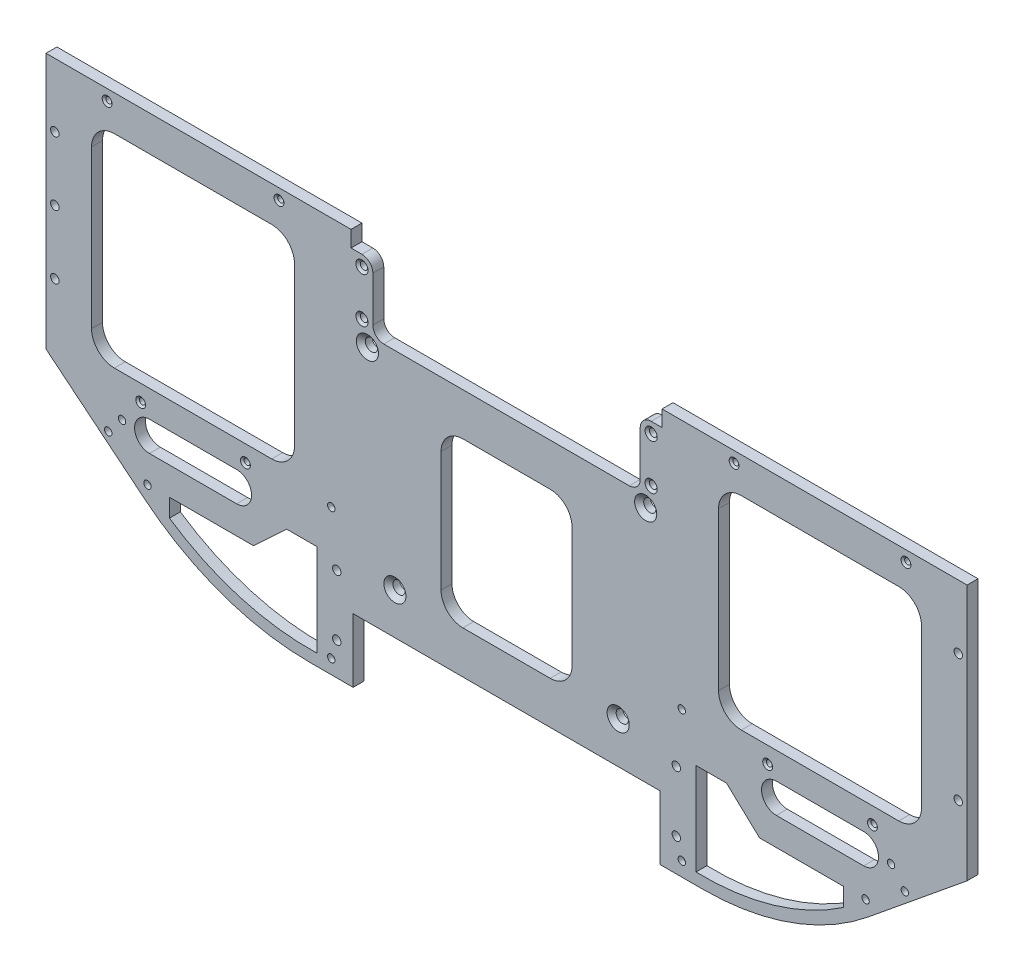
SolidWorks part; units mm, degrees
material "Acrylic (Medium-high impact)"
ref_plane "Front Plane" through (0, 0, 0) normal (0, 0, 1) x (1, 0, 0)
ref_plane "Top Plane" through (0, 0, 0) normal (0, 1, 0) x (1, 0, 0)
ref_plane "Right Plane" through (0, 0, 0) normal (1, 0, 0) x (0, 0, -1)
sketch "Sketch1" plane through (0, 0, 0) normal (0, 0, 1) x (1, 0, 0)
  line L0 (-85.5662, -233.3625) -> (-68.1037, -233.3625) construction
  line L1 (131.2863, 23.8125) -> (131.2863, -87.3125) construction
  line L2 (85.5663, 23.8125) -> (131.2863, 23.8125) construction
  line L3 (85.5663, -144.4625) -> (85.5663, 23.8125) construction
  line L6 (-79.2163, -3.175) -> (79.2162, -3.175) construction
  line L7 (-296.7037, -233.3625) -> (-68.1037, -233.3625)
  line L8 (131.2863, 23.8125) -> (131.2863, -87.3125)
  line L9 (85.5663, 23.8125) -> (131.2863, 23.8125)
  line L10 (85.5663, -3.175) -> (85.5663, 23.8125)
  line L11 (-131.6037, 20.5105) -> (-233.2037, 20.5105)
  line L12 (-131.6037, -3.175) -> (-131.6037, 20.5105)
  line L13 (-131.6037, -3.175) -> (85.5663, -3.175)
  line L14 (95.0913, -144.4625) -> (28.2786, -199.0142)
  line L15 (-182.4037, -196.215) -> (-182.4037, -51.435) construction
  line L16 (-93.5037, -196.215) -> (-271.3037, -196.215) construction
  line L17 (-268.1287, -51.435) -> (-96.6787, -51.435) construction
  line L18 (-459.8987, -144.4625) -> (-393.0861, -199.0142)
  line L19 (-233.2037, -3.175) -> (-450.3737, -3.175)
  line L20 (-233.2037, -3.175) -> (-233.2037, 20.5105)
  line L21 (-450.3737, -3.175) -> (-450.3737, -20.955)
  line L22 (-450.3737, -20.955) -> (-496.0937, -20.955)
  line L23 (-496.0937, -20.955) -> (-496.0937, -87.3125)
  line L24 (-496.0937, -20.955) -> (-450.3737, -20.955) construction
  line L25 (-450.3737, -20.955) -> (-450.3737, -144.4625) construction
  line L26 (-496.0937, -87.3125) -> (-496.0937, -20.955) construction
  arc A0 (-68.1037, -233.3625) -> (28.2786, -199.0142) centre (-68.1037, -80.9625) ccw construction
  arc A1 (95.0913, -144.4625) -> (131.2863, -87.3125) centre (-12.3507, -36.3792) ccw construction
  arc A2 (-68.1037, -233.3625) -> (28.2786, -199.0142) centre (-68.1037, -80.9625) ccw
  arc A3 (95.0913, -144.4625) -> (131.2863, -87.3125) centre (-12.3507, -36.3792) ccw
  arc A4 (-459.8987, -144.4625) -> (-496.0937, -87.3125) centre (-352.4568, -36.3792) cw
  arc A5 (-296.7037, -233.3625) -> (-393.0861, -199.0142) centre (-296.7037, -80.9625) cw
  point P39 (-182.4037, 20.5105)
  point P41 (-182.4037, -233.3625)
extrude "Boss-Extrude1" add sketch "Sketch1" along normal blind 6.35
sketch "Sketch2" plane through (0, 0, 6.35) normal (0, 0, 1) x (1, 0, 0)
  line L0 (-339.4075, -166.116) -> (-390.2075, -166.116) construction
  line L4 (-423.8625, -37.0786) -> (-423.8625, -128.6564)
  line L5 (-319.0186, -23.8125) -> (-410.5964, -23.8125)
  line L6 (-305.7525, -128.6564) -> (-305.7525, -37.0786)
  line L7 (-410.5964, -141.9225) -> (-319.0186, -141.9225)
  line L8 (-423.8625, -37.0786) -> (-423.8625, -128.6564)
  line L9 (-319.0186, -23.8125) -> (-410.5964, -23.8125)
  line L10 (-305.7525, -128.6564) -> (-305.7525, -37.0786)
  line L11 (-410.5964, -141.9225) -> (-319.0186, -141.9225)
  line L13 (-292.6397, -180.7374) -> (-292.6397, -217.9755) construction
  line L14 (-292.6397, -172.9769) -> (-292.6397, -226.6383)
  line L15 (-325.6433, -187.2504) -> (-310.3471, -172.9769) construction
  line L16 (-370.6622, -190.9763) -> (-337.9694, -190.9763) construction
  line L17 (-329.6361, -190.9763) -> (-310.3471, -172.9769)
  line L18 (-378.5543, -190.9763) -> (-329.6361, -190.9763)
  line L19 (-310.3471, -172.9769) -> (-292.6397, -172.9769)
  line L20 (-378.5543, -201.538) -> (-378.5543, -190.9763)
  line L21 (-339.4075, -174.752) -> (-390.2075, -174.752)
  line L24 (-339.4075, -157.48) -> (-390.2075, -157.48)
  line L25 (-182.4037, 20.5105) -> (-182.4037, -233.3625) construction
  line L26 (-131.6037, 20.5105) -> (-233.2037, 20.5105) construction
  line L29 (-296.7037, -233.3625) -> (-68.1037, -233.3625) construction
  line L30 (-25.4, -166.116) -> (25.4, -166.116) construction
  line L31 (-25.4, -174.752) -> (25.4, -174.752)
  line L32 (-25.4, -157.48) -> (25.4, -157.48)
  line L33 (13.7468, -201.538) -> (13.7468, -190.9763)
  line L34 (-54.4604, -172.9769) -> (-72.1678, -172.9769)
  line L35 (13.7468, -190.9763) -> (-35.1714, -190.9763)
  line L36 (-35.1714, -190.9763) -> (-54.4604, -172.9769)
  line L37 (-72.1678, -172.9769) -> (-72.1678, -226.6383)
  line L38 (45.7889, -141.9225) -> (-45.7889, -141.9225)
  line L39 (-59.055, -128.6564) -> (-59.055, -37.0786)
  line L40 (-45.7889, -23.8125) -> (45.7889, -23.8125)
  line L41 (59.055, -37.0786) -> (59.055, -128.6564)
  arc A4 (-423.8625, -128.6564) -> (-410.5964, -141.9225) centre (-410.5964, -128.6564) ccw
  arc A5 (-410.5964, -23.8125) -> (-423.8625, -37.0786) centre (-410.5964, -37.0786) ccw
  arc A6 (-305.7525, -37.0786) -> (-319.0186, -23.8125) centre (-319.0186, -37.0786) ccw
  arc A7 (-319.0186, -141.9225) -> (-305.7525, -128.6564) centre (-319.0186, -128.6564) ccw
  arc A8 (-423.8625, -128.6564) -> (-410.5964, -141.9225) centre (-410.5964, -128.6564) ccw
  arc A9 (-410.5964, -23.8125) -> (-423.8625, -37.0786) centre (-410.5964, -37.0786) ccw
  arc A10 (-305.7525, -37.0786) -> (-319.0186, -23.8125) centre (-319.0186, -37.0786) ccw
  arc A11 (-319.0186, -141.9225) -> (-305.7525, -128.6564) centre (-319.0186, -128.6564) ccw
  arc A13 (-339.4075, -174.752) -> (-339.4075, -157.48) centre (-339.4075, -166.116) ccw
  arc A15 (-373.3334, -204.9216) -> (-339.4598, -220.2819) centre (-296.7037, -80.9625) ccw construction
  arc A17 (-378.5543, -201.538) -> (-292.6397, -226.6383) centre (-296.7037, -80.9625) ccw
  arc A19 (-390.2075, -157.48) -> (-390.2075, -174.752) centre (-390.2075, -166.116) ccw
  arc A20 (-25.4, -174.752) -> (-25.4, -157.48) centre (-25.4, -166.116) cw
  arc A21 (25.4, -157.48) -> (25.4, -174.752) centre (25.4, -166.116) cw
  arc A22 (13.7468, -201.538) -> (-72.1678, -226.6383) centre (-68.1038, -80.9625) cw
  arc A23 (-45.7889, -141.9225) -> (-59.055, -128.6564) centre (-45.7889, -128.6564) cw
  arc A24 (-59.055, -37.0786) -> (-45.7889, -23.8125) centre (-45.7889, -37.0786) cw
  arc A25 (45.7889, -23.8125) -> (59.055, -37.0786) centre (45.7889, -37.0786) cw
  arc A26 (59.055, -128.6564) -> (45.7889, -141.9225) centre (45.7889, -128.6564) cw
  point P10 (-364.8075, -166.116)
  point P27 (0, -166.116)
  dimension "D2" = 8.636
  dimension "D3" = 50.8
  dimension "D1" = 0
extrude "Cut-Extrude1" cut sketch "Sketch2" against normal through all
hole_wizard "CSK for 1/4 Flat Head Machine Screw (100)1" positions "Sketch3" profile "Sketch4" countersink size "1/4" standard "ANSI Inch" end condition up to next
sketch "Sketch3" plane through (0, 0, 6.35) normal (0, 0, 1) x (1, 0, 0)
  point P0 (-247.3642, -172.085)
  point P3 (-263.3662, -57.785)
  point P6 (-117.4432, -172.085)
  point P9 (-101.4412, -57.785)
sketch "Sketch4" plane through (-247.3642, -172.085, 6.35) normal (1, 0, 0) x (0, -1, 0)
  line L0 (0, 0) -> (0, 6.35)
  line L1 (0, 6.35) -> (3.5712, 6.35)
  line L2 (3.5712, 6.35) -> (3.5712, 2.4063)
  line L3 (3.5712, 2.4063) -> (6.4389, 0)
  line L5 (6.4389, 0) -> (0, 0)
  line L6 (-3.5712, 2.4063) -> (-6.4389, 0) construction
  line L11 (0, -6.35) -> (0, 107.95) construction
  dimension "Thru Hole Dia." = 7.1425
  dimension "Thru Hole Depth" = 6.35
  dimension "Near C'Sink Dia." = 12.8778
  dimension "Near C'Sink Angle" = 100
hole_wizard "CSK for #4 Flat Head Machine Screw (100)1" positions "Sketch5" profile "Sketch6" countersink size "#4" standard "ANSI Inch" end condition through all
sketch "Sketch5" plane through (0, 0, 6.35) normal (0, 0, 1) x (1, 0, 0)
  point P0 (-334.3275, -151.5305)
  point P3 (-395.2875, -151.5305)
  point P6 (-314.8013, -9.525)
  point P9 (-414.8137, -9.525)
  point P12 (30.48, -151.5305)
  point P15 (-30.48, -151.5305)
  point P18 (50.0062, -9.525)
  point P21 (-50.0062, -9.525)
sketch "Sketch6" plane through (-334.3275, -151.5305, 6.35) normal (1, 0, 0) x (0, -1, 0)
  line L0 (0, 0) -> (0, 6.35)
  line L1 (0, 6.35) -> (1.7272, 6.35)
  line L2 (1.7272, 6.35) -> (1.7272, 0.9484)
  line L3 (1.7272, 0.9484) -> (2.8575, 0)
  line L5 (2.8575, 0) -> (0, 0)
  line L6 (-1.7272, 0.9484) -> (-2.8575, 0) construction
  line L11 (0, -6.35) -> (0, 107.95) construction
  dimension "Thru Hole Dia." = 3.4544
  dimension "Thru Hole Depth" = 6.35
  dimension "Near C'Sink Dia." = 5.715
  dimension "Near C'Sink Angle" = 100
sketch "Sketch7" plane through (0, 0, 6.35) normal (0, 0, 1) x (1, 0, 0)
  line L0 (-271.672, -233.3625) -> (-271.672, -196.215)
  line L1 (-271.672, -196.215) -> (-93.1354, -196.215)
  line L2 (-182.4037, -196.215) -> (-182.4037, -233.3625) construction
  line L3 (-296.7037, -233.3625) -> (-68.1037, -233.3625) construction
  line L4 (-93.5037, -196.215) -> (-271.3037, -196.215) construction
  line L5 (-93.1354, -233.3625) -> (-271.672, -233.3625)
  line L6 (-93.1354, -233.3625) -> (-93.1354, -196.215)
extrude "Cut-Extrude2" cut sketch "Sketch7" against normal up to next
hole_wizard "#6 Clearance Hole1" positions "Sketch21" profile "Sketch31" hole size "#6" standard "ANSI Inch" end condition up to next
sketch "Sketch21" plane through (-452.3171, -175.5643, 0) normal (0, 0, -1) x (-1, 0, 0)
  point P0 (-60.9984, -15.4755)
  point P3 (-167.9324, -49.5432)
  point P6 (-167.9324, 26.727)
  point P9 (-371.8944, 26.727)
  point P12 (-371.8944, -49.5432)
  point P15 (-478.8284, -15.4755)
sketch "Sketch31" plane through (-391.3187, -191.0398, 0) normal (1, 0, 0) x (0, 1, 0)
  line L0 (0, 0) -> (0, 6.35)
  line L1 (0, 6.35) -> (2.1526, 6.35)
  line L2 (2.1526, 6.35) -> (2.1526, 0)
  line L5 (2.1526, 0) -> (0, 0)
  line L11 (0, -6.35) -> (0, 107.95) construction
  dimension "Thru Hole Dia." = 4.3053
  dimension "Thru Hole Depth" = 6.35
hole_wizard "#6 Plastic Insert" positions "Sketch41" profile "Sketch51" legacy
sketch "Sketch41" plane through (-452.3171, -175.5643, 0) normal (0, 0, -1) x (-1, 0, 0)
  point P0 (-60.9984, -15.4755)
  point P3 (-167.9324, -49.5432)
  point P6 (-167.9324, 26.727)
  point P9 (-371.8944, 26.727)
  point P12 (-371.8944, -49.5432)
  point P15 (-478.8284, -15.4755)
sketch "Sketch51" plane through (-391.3187, -191.0398, 0) normal (1, 0, 0) x (0, 1, 0)
  line L0 (0, 0) -> (0, 3.81)
  line L1 (0, 3.81) -> (2.5273, 3.81)
  line L2 (2.5273, 3.81) -> (2.6543, 0)
  line L3 (2.6543, 0) -> (0, 0)
  line L4 (0, 110) -> (0, -10) construction
  dimension "Minor Diameter" = 5.0546
  dimension "Depth" = 3.81
  dimension "Major Diameter" = 5.3086
other "#6 Plastic Insert Hole<1>"
hole_wizard "#6 Clearance Hole2" positions "Sketch52" profile "Sketch53" hole size "#6" standard "ANSI Inch" end condition through all
sketch "Sketch52" plane through (0, 0, 0) normal (0, 0, -1) x (-1, 0, 0)
  point P0 (459.5177, -126.1745)
  point P3 (479.9012, -91.8845)
  point P6 (486.5052, -36.449)
  point P9 (-94.7103, -126.1745)
  point P12 (-121.9518, -83.6295)
  point P15 (-98.2663, 15.875)
sketch "Sketch53" plane through (-459.5177, -126.1745, 0) normal (1, 0, 0) x (0, 1, 0)
  line L0 (0, 0) -> (0, 6.35)
  line L1 (0, 6.35) -> (2.1526, 6.35)
  line L2 (2.1526, 6.35) -> (2.1526, 0)
  line L5 (2.1526, 0) -> (0, 0)
  line L11 (0, -6.35) -> (0, 107.95) construction
  dimension "Thru Hole Dia." = 4.3053
  dimension "Thru Hole Depth" = 6.35
sketch "Sketch54" plane through (0, 0, 6.35) normal (0, 0, 1) x (1, 0, 0)
  line L0 (-91.9162, -51.435) -> (-272.8912, -51.435) construction
  line L1 (-93.5037, -49.8475) -> (-271.3037, -49.8475) construction
  line L2 (-93.5037, -49.8475) -> (-93.5037, 20.5105) construction
  line L3 (-93.5037, 20.5105) -> (-271.3037, 20.5105) construction
  line L4 (-271.3037, -49.8475) -> (-271.3037, 20.5105) construction
  line L7 (-131.6037, 20.5105) -> (-233.2037, 20.5105) construction
  line L8 (-272.8912, -38.735) -> (-260.1912, -38.735)
  line L9 (-260.1912, -51.435) -> (-260.1912, -38.735)
  line L10 (-104.6162, -51.435) -> (-260.1912, -51.435)
  line L11 (-272.8912, -38.735) -> (-272.8912, 22.098)
  line L12 (-91.9162, 22.098) -> (-272.8912, 22.098)
  line L13 (-91.9162, -38.735) -> (-91.9162, 22.098)
  line L14 (-272.8912, -51.435) -> (-272.8912, 22.098) construction
  line L17 (-91.9162, -38.735) -> (-104.6162, -38.735)
  line L18 (-104.6162, -51.435) -> (-104.6162, -38.735)
  line L19 (-91.9162, -51.435) -> (-91.9162, 22.098) construction
  dimension "D1" = 1.5875
  dimension "D2" = 12.7
  dimension "D3" = 12.7
  dimension "D4" = 12.7
  dimension "D5" = 12.7
extrude "Cut-Extrude3" cut sketch "Sketch54" against normal up to next
sketch "Sketch55" plane through (0, 0, 6.35) normal (0, 0, 1) x (1, 0, 0)
  line L0 (-91.9162, -38.735) -> (-91.9162, -3.175) construction
  line L1 (-91.9162, -12.572) -> (-104.6162, -12.572)
  line L2 (-91.9162, -12.572) -> (-91.9162, -38.735)
  line L3 (-91.9162, -38.735) -> (-104.6162, -38.735)
  line L4 (-104.6162, -12.572) -> (-104.6162, -38.735)
  line L6 (-182.4037, -51.435) -> (-182.4037, -196.215) construction
  line L7 (-260.1912, -51.435) -> (-104.6162, -51.435) construction
  line L8 (-93.1354, -196.215) -> (-271.672, -196.215) construction
  line L9 (-260.1912, -12.572) -> (-260.1912, -38.735)
  line L10 (-272.8912, -38.735) -> (-260.1912, -38.735)
  line L11 (-272.8912, -12.572) -> (-272.8912, -38.735)
  line L12 (-272.8912, -12.572) -> (-260.1912, -12.572)
  line L13 (-93.5037, -9.397) -> (-134.7787, -9.397) construction
  dimension "D1" = 12.7
  dimension "D2" = 3.175
extrude "Boss-Extrude2" add sketch "Sketch55" against normal through all
fillet "Fillet3" radius 6.35 4 edges at (-104.6162, -12.572, 3.175) (-104.6162, -51.435, 3.175) (-260.1912, -51.435, 3.175) (-260.1912, -12.572, 3.175)
hole_wizard "CSK for #6 Flat Head Machine Screw (100)1" positions "Sketch56" profile "Sketch57" countersink size "#6" standard "ANSI Inch" end condition through all
sketch "Sketch56" plane through (0, 0, 6.35) normal (0, 0, 1) x (1, 0, 0)
  line L0 (-110.5963, -40.514) -> (-110.5963, -49.8475) construction
  line L2 (-95.0912, -49.8475) -> (-161.4487, -49.8475) construction
  line L3 (-103.0287, -40.514) -> (-110.5963, -40.514) construction
  line L4 (-110.5963, -45.1807) -> (-98.2662, -45.1807) construction
  point P0 (-266.5412, -18.922)
  point P8 (-98.2662, -18.922)
  point P31 (-98.2662, -45.1807)
  point P32 (-266.5412, -45.1807)
sketch "Sketch57" plane through (-266.5412, -18.922, 6.35) normal (1, 0, 0) x (0, -1, 0)
  line L0 (0, 0) -> (0, 6.35)
  line L1 (0, 6.35) -> (2.1526, 6.35)
  line L2 (2.1526, 6.35) -> (2.1526, 1.1669)
  line L3 (2.1526, 1.1669) -> (3.5433, 0)
  line L5 (3.5433, 0) -> (0, 0)
  line L6 (-2.1526, 1.1669) -> (-3.5433, 0) construction
  line L11 (0, -6.35) -> (0, 107.95) construction
  dimension "Thru Hole Dia." = 4.3053
  dimension "Thru Hole Depth" = 6.35
  dimension "Near C'Sink Dia." = 7.0866
  dimension "Near C'Sink Angle" = 100
sketch "Sketch58" plane through (0, 0, 6.35) normal (0, 0, 1) x (1, 0, 0)
  line L1 (-201.4537, -123.825) -> (-163.3537, -123.825) construction
  line L2 (-144.3037, -171.45) -> (-220.5037, -171.45)
  line L3 (-144.3037, -171.45) -> (-144.3037, -76.2)
  line L4 (-144.3037, -76.2) -> (-220.5037, -76.2)
  line L5 (-182.4037, -95.25) -> (-182.4037, -152.4) construction
  line L6 (-163.3537, -95.25) -> (-163.3537, -152.4) construction
  line L7 (-201.4537, -95.25) -> (-201.4537, -152.4) construction
  line L8 (-220.5037, -171.45) -> (-220.5037, -76.2)
  line L9 (-144.3037, -171.45) -> (-220.5037, -76.2) construction
  line L10 (-144.3037, -76.2) -> (-220.5037, -171.45) construction
  arc A0 (-163.3537, -95.25) -> (-201.4537, -95.25) centre (-182.4037, -95.25) ccw construction
  arc A1 (-201.4537, -152.4) -> (-163.3537, -152.4) centre (-182.4037, -152.4) ccw construction
  point P0 (-182.4037, -123.825)
  point P9 (-182.4037, -123.825)
  dimension "D1" = 57.15
  dimension "D2" = 38.1
  dimension "D3" = 76.2
extrude "Cut-Extrude4" cut sketch "Sketch58" against normal through all
sketch "Sketch60" plane through (0, 0, 6.35) normal (0, 0, 1) x (1, 0, 0)
  line L0 (85.5663, 23.8125) -> (85.5663, -152.2395)
  line L1 (28.2786, -199.0142) -> (95.0913, -144.4625) construction
  line L2 (131.2863, 23.8125) -> (85.5663, 23.8125) construction
  line L3 (131.2863, -87.3125) -> (131.2863, 23.8125) construction
  line L4 (131.2863, 23.8125) -> (85.5663, 23.8125)
  line L5 (131.2863, -87.3125) -> (131.2863, 23.8125)
  line L6 (85.5663, -152.2395) -> (95.0913, -144.4625)
  line L7 (-450.3737, -20.955) -> (-496.0937, -20.955) construction
  line L8 (-496.0937, -20.955) -> (-496.0937, -87.3125) construction
  line L9 (-459.8987, -144.4625) -> (-393.0861, -199.0142) construction
  line L10 (-450.3737, -20.955) -> (-496.0937, -20.955)
  line L11 (-496.0937, -20.955) -> (-496.0937, -87.3125)
  line L12 (-459.8987, -144.4625) -> (-450.3737, -152.2395)
  line L13 (-450.3737, -20.955) -> (-450.3737, -152.2395)
  arc A0 (95.0913, -144.4625) -> (131.2863, -87.3125) centre (-12.3507, -36.3792) ccw construction
  arc A1 (95.0913, -144.4625) -> (131.2863, -87.3125) centre (-12.3507, -36.3792) ccw
  arc A2 (-496.0937, -87.3125) -> (-459.8987, -144.4625) centre (-352.4568, -36.3792) ccw construction
  arc A3 (-496.0937, -87.3125) -> (-459.8987, -144.4625) centre (-352.4568, -36.3792) ccw
extrude "Cut-Extrude5" cut sketch "Sketch60" against normal through all
hole_wizard "CSK for #8 Flat Head Machine Screw (100)2" positions "Sketch61" profile "Sketch62" countersink size "#8" standard "ANSI Inch" end condition up to next
sketch "Sketch61" plane through (0, 0, 0) normal (0, 0, -1) x (-1, 0, 0)
  line L0 (281.197, -160.0558) -> (281.197, -233.3625) construction
  line L1 (296.7037, -233.3625) -> (271.672, -233.3625) construction
  line L5 (271.672, -186.69) -> (182.4037, -186.69) construction
  line L6 (182.4037, -186.69) -> (93.1355, -186.69) construction
  line L9 (445.2302, -3.175) -> (445.2302, -77.2147) construction
  line L10 (445.2302, -77.2147) -> (445.2302, -151.2545) construction
  line L11 (182.4037, -196.215) -> (182.4037, -51.435) construction
  line L12 (271.672, -196.215) -> (93.1354, -196.215) construction
  line L13 (110.9662, -51.435) -> (253.8412, -51.435) construction
  line L15 (-80.4228, -77.2147) -> (-80.4228, -151.2545) construction
  line L16 (-80.4228, -3.175) -> (-80.4228, -77.2147) construction
  line L17 (93.1355, -186.69) -> (182.4037, -186.69) construction
  line L18 (83.6104, -160.0558) -> (83.6104, -233.3625) construction
  point P0 (281.197, -214.3125)
  point P2 (281.197, -179.1058)
  point P36 (445.2302, -77.2147)
  point P41 (445.2302, -40.1949)
  point P45 (445.2302, -114.2346)
  point P61 (-80.4228, -114.2346)
  point P62 (-80.4228, -40.1949)
  point P64 (83.6104, -179.1058)
  point P65 (83.6104, -214.3125)
  dimension "D1" = 19.05
  dimension "D2" = 19.05
sketch "Sketch62" plane through (-281.197, -214.3125, 0) normal (1, 0, 0) x (0, 1, 0)
  line L0 (0, 0) -> (0, 6.35)
  line L1 (0, 6.35) -> (2.4574, 6.35)
  line L2 (2.4574, 6.35) -> (2.4574, 1.4759)
  line L3 (2.4574, 1.4759) -> (4.2164, 0)
  line L5 (4.2164, 0) -> (0, 0)
  line L6 (-2.4574, 1.4759) -> (-4.2164, 0) construction
  line L11 (0, -6.35) -> (0, 107.95) construction
  dimension "Thru Hole Dia." = 4.9149
  dimension "Thru Hole Depth" = 6.35
  dimension "Near C'Sink Dia." = 8.4328
  dimension "Near C'Sink Angle" = 100
fillet "Fillet4" radius 12.7 4 edges at (-144.3037, -171.45, 3.175) (-144.3037, -76.2, 3.175) (-220.5037, -76.2, 3.175) (-220.5037, -171.45, 3.175)
hole_wizard "CSK for #6 Flat Head Machine Screw (100)2" positions "Sketch63" profile "Sketch64" countersink size "#6" standard "ANSI Inch" end condition up to next
sketch "Sketch63" plane through (0, 0, 0) normal (0, 0, -1) x (-1, 0, 0)
  circle A0 centre (406.1283, -165.8215) radius 2.1527 construction
  circle A1 centre (414.1604, -175.659) radius 2.1527 construction
  circle A2 centre (-41.3183, -165.8233) radius 2.1526 construction
  circle A3 centre (-49.3504, -175.6607) radius 2.1527 construction
  point P0 (414.1604, -175.659)
  point P2 (406.1283, -165.8215)
  point P10 (-41.3183, -165.8233)
  point P12 (-49.3504, -175.6607)
sketch "Sketch64" plane through (-414.1604, -175.659, 0) normal (1, 0, 0) x (0, 1, 0)
  line L0 (0, 0) -> (0, 6.35)
  line L1 (0, 6.35) -> (2.1526, 6.35)
  line L2 (2.1526, 6.35) -> (2.1526, 1.1669)
  line L3 (2.1526, 1.1669) -> (3.5433, 0)
  line L5 (3.5433, 0) -> (0, 0)
  line L6 (-2.1526, 1.1669) -> (-3.5433, 0) construction
  line L11 (0, -6.35) -> (0, 107.95) construction
  dimension "Thru Hole Dia." = 4.3053
  dimension "Thru Hole Depth" = 6.35
  dimension "Near C'Sink Dia." = 7.0866
  dimension "Near C'Sink Angle" = 100
